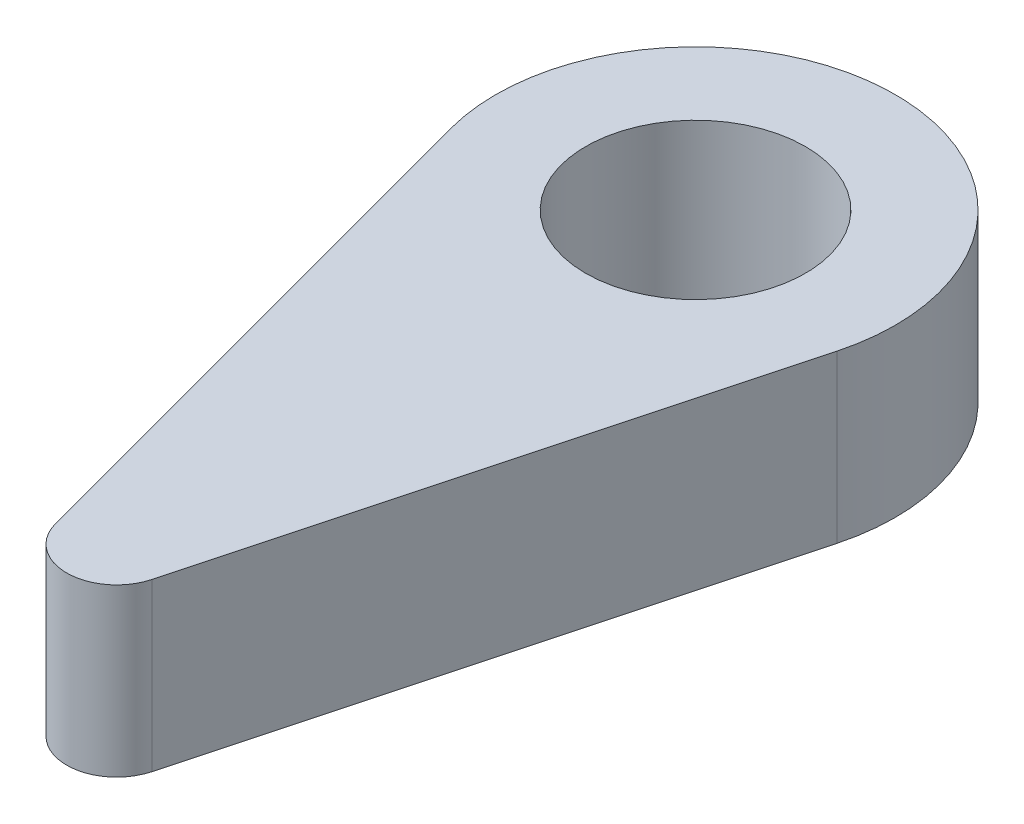
SolidWorks part; units mm, degrees
material "1023 탄소 강판(SS)"
ref_plane "정면" through (0, 0, 0) normal (0, 0, 1) x (1, 0, 0)
ref_plane "윗면" through (0, 0, 0) normal (0, 1, 0) x (1, 0, 0)
ref_plane "우측면" through (0, 0, 0) normal (1, 0, 0) x (0, 0, -1)
sketch "스케치1" plane through (0, 0, 0) normal (0, 1, 0) x (1, 0, 0)
  line L0 (-1.4489, -17.7749) -> (-5.7956, -1.5529)
  line L1 (1.4489, -17.7749) -> (5.7956, -1.5529)
  circle A0 centre (0, 0) radius 3.3
  circle A1 centre (0, 0) radius 6
  arc A2 (-1.4489, -17.7749) -> (1.4489, -17.7749) centre (0, -17.3867) ccw
  dimension "D1" = 6.6
  dimension "D2" = 12
  dimension "D4" = 3
  dimension "D3" = 30
extrude "보스-돌출1" add sketch "스케치1" along normal blind 5 contours A1 A0 | L0 A2 L1 A1
